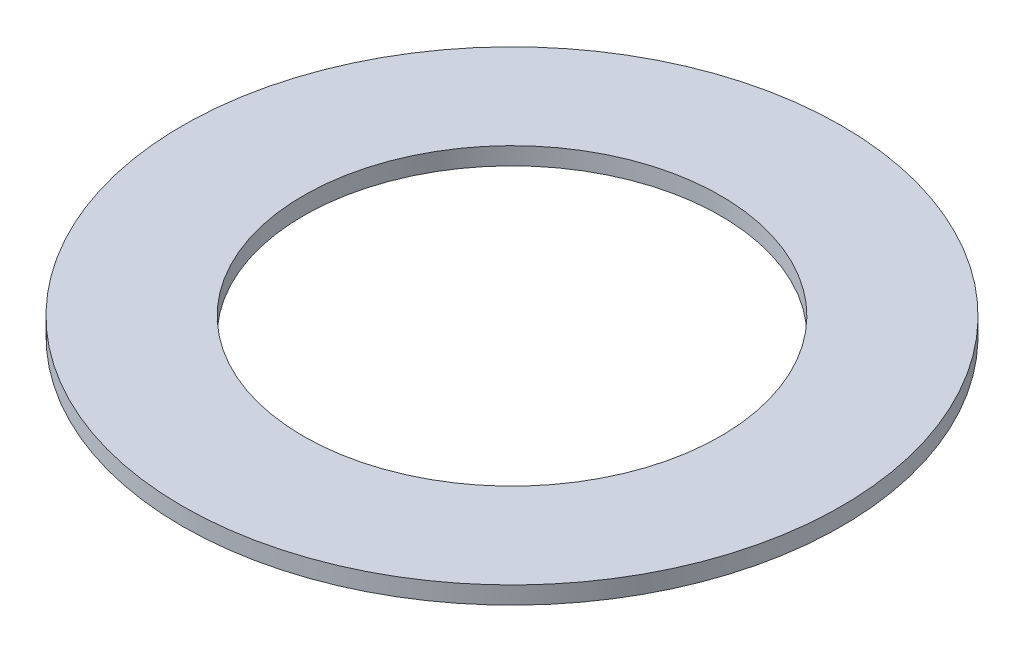
SolidWorks part; units mm, degrees
ref_plane "Front Plane" through (0, 0, 0) normal (0, 0, 1) x (1, 0, 0)
ref_plane "Top Plane" through (0, 0, 0) normal (0, 1, 0) x (1, 0, 0)
ref_plane "Right Plane" through (0, 0, 0) normal (1, 0, 0) x (0, 0, -1)
sketch "Sketch1" plane through (0, 0, 0) normal (0, 1, 0) x (1, 0, 0)
  circle A0 centre (0, 0) radius 5.65
  circle A1 centre (0, 0) radius 3.575
  dimension "D1" = 11.3
  dimension "D2" = 7.15
extrude "Boss-Extrude1" add sketch "Sketch1" along normal blind 0.3
